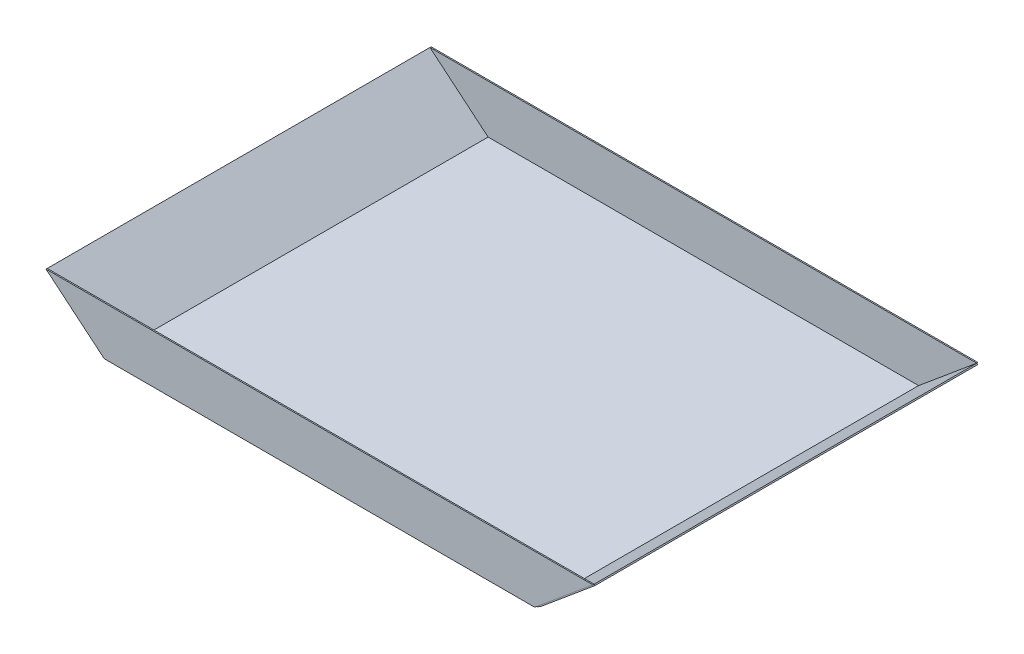
SolidWorks part; units mm, degrees
ref_plane "Front Plane" through (0, 0, 0) normal (0, 0, 1) x (1, 0, 0)
ref_plane "Top Plane" through (0, 0, 0) normal (0, 1, 0) x (1, 0, 0)
ref_plane "Right Plane" through (0, 0, 0) normal (1, 0, 0) x (0, 0, -1)
sketch "Sketch1" plane through (0, 0, 0) normal (0, 0, 1) x (1, 0, 0)
  line L0 (-76.2902, 63.5852) -> (0, 0)
  line L1 (0, 0) -> (564.261, 0)
  line L2 (564.261, 0) -> (640.5512, 63.5852)
  dimension "D1" = 564.261
  dimension "D2" = 99.314
  dimension "D3" = 99.314
  dimension "D4" = 140.19
  dimension "D5" = 140.19
extrude "Extrude-Thin1" add sketch "Sketch1" along normal blind 501.65 thin
fillet "Fillet1" radius 25.4 2 edges at (-0.5748, -1.5875, 250.825) (564.8358, -1.5875, 250.825)
sketch "Sketch2" plane through (0, 0, 501.65) normal (0, 0, 1) x (1, 0, 0)
  line L0 (-76.2902, 63.5852) -> (640.5512, 63.5852)
  line L1 (640.5512, 63.5852) -> (564.261, 0)
  line L2 (564.261, 0) -> (0, 0)
  line L3 (0, 0) -> (-76.2902, 63.5852)
extrude "Boss-Extrude1" add sketch "Sketch2" along normal blind 1.5875 separate body
sketch "Sketch3" plane through (0, 0, 0) normal (0, 0, -1) x (-1, 0, 0)
  line L0 (-640.5512, 63.5852) -> (76.2902, 63.5852)
  line L1 (76.2902, 63.5852) -> (0, 0)
  line L2 (0, 0) -> (-564.261, 0)
  line L3 (-564.261, 0) -> (-640.5512, 63.5852)
extrude "Boss-Extrude2" add sketch "Sketch3" along normal blind 1.5875 separate body
